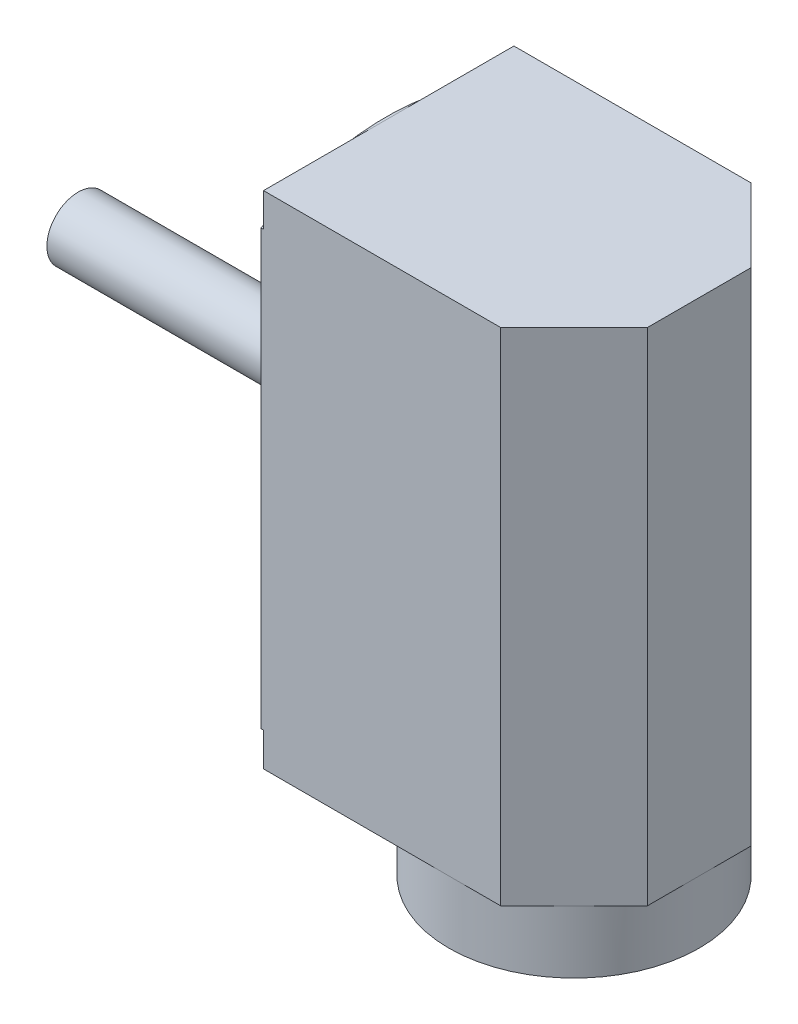
SolidWorks part; units mm, degrees
material "Cast Alloy Steel"
ref_plane "Front Plane" through (0, 0, 0) normal (0, 0, 1) x (1, 0, 0)
ref_plane "Top Plane" through (0, 0, 0) normal (0, 1, 0) x (1, 0, 0)
ref_plane "Right Plane" through (0, 0, 0) normal (1, 0, 0) x (0, 0, -1)
sketch "Sketch1" plane through (0, 0, 0) normal (0, 1, 0) x (1, 0, 0)
  line L0 (0, -6.35) -> (0, 6.35)
  line L1 (0, 6.35) -> (12.1553, 6.35)
  line L2 (12.1553, 6.35) -> (15.875, 2.6303)
  line L3 (15.875, 2.6303) -> (15.875, -2.6303)
  line L4 (15.875, -2.6303) -> (12.1553, -6.35)
  line L5 (12.1553, -6.35) -> (0, -6.35)
  line L6 (0, 0) -> (15.875, 0) construction
  circle A0 centre (9.525, 0) radius 6.35 construction
  point P3 (15.875, 0)
  point P12 (0, 0)
  dimension "D1" = 12.7
  dimension "D2" = 15.875
  dimension "D3" = 45
  dimension "D4" = 45
  dimension "D5" = 9.525
extrude "Boss-Extrude1" add sketch "Sketch1" along normal blind 25.4
sketch "Sketch2" plane through (0, 0, 0) normal (0, -1, 0) x (1, 0, 0)
  circle A0 centre (9.525, 0) radius 4.7625
  circle A2 centre (9.525, 0) radius 6.35
  dimension "D1" = 9.525
  dimension "D3" = 12.7
  dimension "D2" = 9.525
extrude "Boss-Extrude2" add sketch "Sketch2" along normal blind 3.175
sketch "Sketch3" plane through (0, -3.175, 0) normal (0, -1, 0) x (1, 0, 0)
  circle A0 centre (9.525, 0) radius 4.7625
  dimension "D1" = 9.525
extrude "Cut-Extrude1" cut sketch "Sketch3" against normal blind 26.1937
sketch "Sketch4" plane through (0, 0, 0) normal (-1, 0, 0) x (0, 0, 1)
  line L0 (-6.35, -3.175) -> (6.35, -3.175) construction
  circle A0 centre (0, 12.7) radius 5.5562
  dimension "D1" = 11.1125
  dimension "D2" = 15.875
extrude "Cut-Extrude2" cut sketch "Sketch4" against normal blind 0.254
sketch "Sketch5" plane through (0.254, 0, 0) normal (-1, 0, 0) x (0, 0, 1)
  circle A0 centre (0, 12.7) radius 1.5875
  dimension "D1" = 3.175
extrude "Boss-Extrude3" add sketch "Sketch5" along normal blind 15.875
sketch "Sketch6" plane through (0, 0, 0) normal (-1, 0, 0) x (0, 0, 1)
  circle A0 centre (0, 22.225) radius 0.7937
  circle A1 centre (0, 12.7) radius 5.5562 construction
  dimension "D2" = 1.5875
  dimension "D1" = 9.525
extrude "Cut-Extrude3" cut sketch "Sketch6" against normal blind 4.572
sketch "Sketch7" plane through (0, 0, 0) normal (-1, 0, 0) x (0, 0, 1)
  line L0 (-6.35, 0) -> (6.35, 0)
  line L3 (6.35, 0) -> (6.35, 1.7015)
  line L4 (6.35, 25.4) -> (6.35, 0) construction
  line L5 (-6.35, 0) -> (-6.35, 1.7015)
  line L6 (-6.35, 25.4) -> (6.35, 25.4)
  line L7 (-6.35, 25.4) -> (6.35, 25.4) construction
  line L8 (6.35, 25.4) -> (6.35, 23.6985)
  line L9 (-6.35, 25.4) -> (-6.35, 23.6985)
  line L10 (-6.35, 25.4) -> (-6.35, 0) construction
  arc A0 (-6.35, 1.7015) -> (6.35, 1.7015) centre (0, 12.7) ccw
  arc A1 (6.35, 23.6985) -> (-6.35, 23.6985) centre (0, 12.7) ccw
  line M4 (-6.35, 0) -> (6.35, 0)
  line M5 (6.35, 0) -> (6.35, 25.4)
  line M6 (6.35, 25.4) -> (-6.35, 25.4)
  line M7 (-6.35, 25.4) -> (-6.35, 0)
  dimension "D1" = 25.4
extrude "Cut-Extrude4" cut sketch "Sketch7" against normal blind 0.127 contours A1 M5 M6 | A1 L6 M7 | A0 M7 M4 | A0 L0 M5
